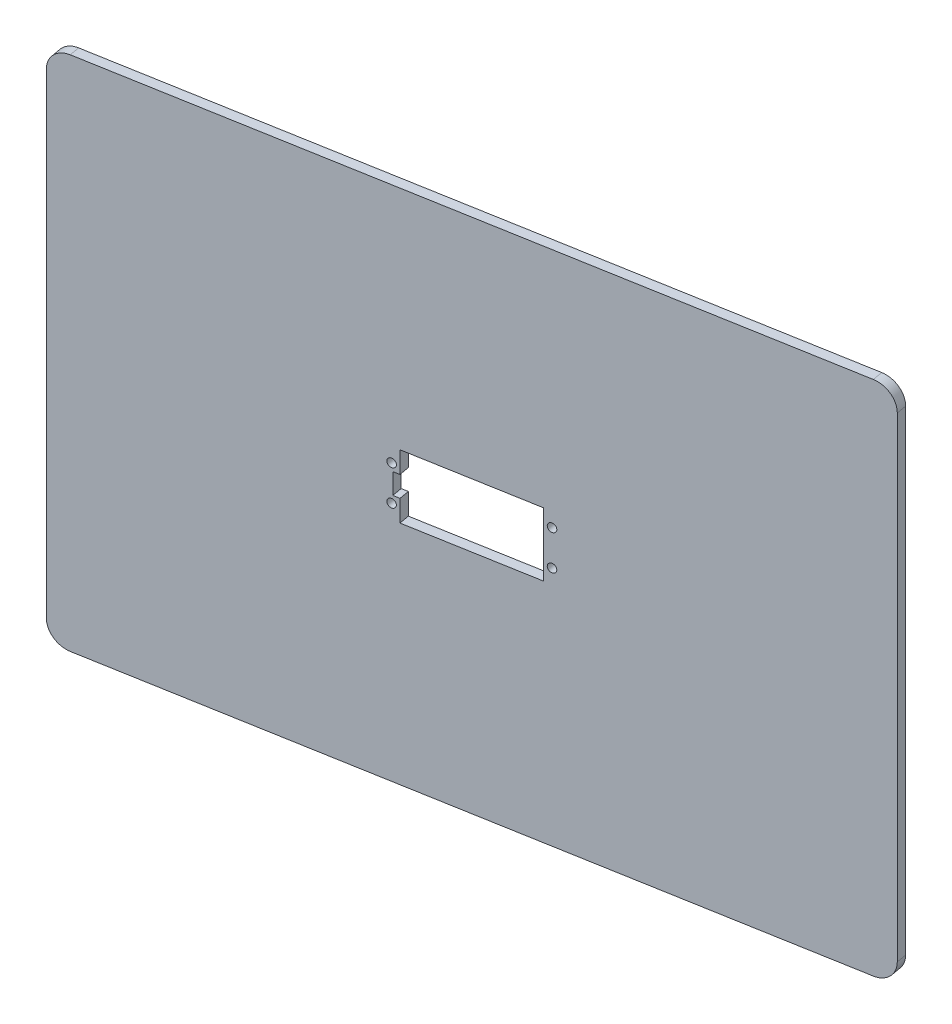
SolidWorks part; units mm, degrees
material "Acrylic (Medium-high impact)"
ref_plane "Front Plane" through (0, 0, 0) normal (0, 0, 1) x (1, 0, 0)
ref_plane "Top Plane" through (0, 0, 0) normal (0, 1, 0) x (1, 0, 0)
ref_plane "Right Plane" through (0, 0, 0) normal (1, 0, 0) x (0, 0, -1)
sketch "Sketch1" plane through (-21.3399, 0, -121.0248) normal (-0.1736, 0, -0.9848) x (-0.9848, 0, 0.1736)
  line L0 (-170.7143, 113.7712) -> (164.3765, 113.7712) construction
  line L1 (-182.6319, -136.2288) -> (172.7675, -136.2288)
  line L2 (-182.6319, -136.2288) -> (-182.6319, 113.7712)
  line L3 (-182.6319, 113.7712) -> (172.7675, 113.7712)
  line L4 (172.7675, -136.2288) -> (172.7675, 113.7712)
  line L7 (-170.7143, -136.2288) -> (164.3765, -136.2288) construction
extrude "Boss-Extrude1" add sketch "Sketch1" along normal blind 5
sketch "Sketch2" plane through (-21.3399, 0, -121.0248) normal (0.1736, 0, 0.9848) x (0.9848, 0, -0.1736)
  line L0 (4.9322, 113.7712) -> (4.9322, -102.7824) construction
  line L1 (-172.7675, 113.7712) -> (182.6319, 113.7712) construction
  line L2 (182.6319, -11.2288) -> (-147.4922, -11.2288) construction
  line L3 (182.6319, 113.7712) -> (182.6319, -136.2288) construction
  line L4 (-25.0678, -16.2288) -> (-25.0678, -26.5788)
  line L5 (-25.0678, 4.1212) -> (34.9322, 4.1212)
  line L6 (-25.0678, 4.1212) -> (-25.0678, -6.2288)
  line L7 (-25.0678, -26.5788) -> (34.9322, -26.5788)
  line L8 (34.9322, 4.1212) -> (34.9322, -26.5788)
  line L9 (-25.0678, 4.1212) -> (34.9322, -26.5788) construction
  line L10 (-25.0678, -26.5788) -> (34.9322, 4.1212) construction
  line L11 (-25.0678, -6.2288) -> (-28.0678, -6.2288)
  line L13 (-25.0678, -16.2288) -> (-28.0678, -16.2288)
  line L14 (-28.0678, -6.2288) -> (-28.0678, -16.2288)
  point P18 (-28.0678, -11.2288)
  dimension "D2" = 60
  dimension "D3" = 30.7
  dimension "D4" = 10
  dimension "D5" = 3
extrude "Cut-Extrude1" cut sketch "Sketch2" against normal blind 10
sketch "Sketch3" plane through (-22.2082, 0, -125.9488) normal (-0.1736, 0, -0.9848) x (-0.9848, 0, 0.1736)
  circle A1 centre (28.5678, -19.6788) radius 2
  circle A2 centre (28.5678, -2.7788) radius 2
  circle A3 centre (-38.4322, -2.7788) radius 2
  circle A4 centre (-38.4322, -19.6788) radius 2
extrude "Cut-Extrude2" cut sketch "Sketch3" against normal blind 5
fillet "Fillet1" radius 10 4 edges at (-191.9168, 113.7712, -93.4861) (-191.9168, -136.2288, -93.4861) (158.0832, -136.2288, -155.2005) (158.0832, 113.7712, -155.2005)
